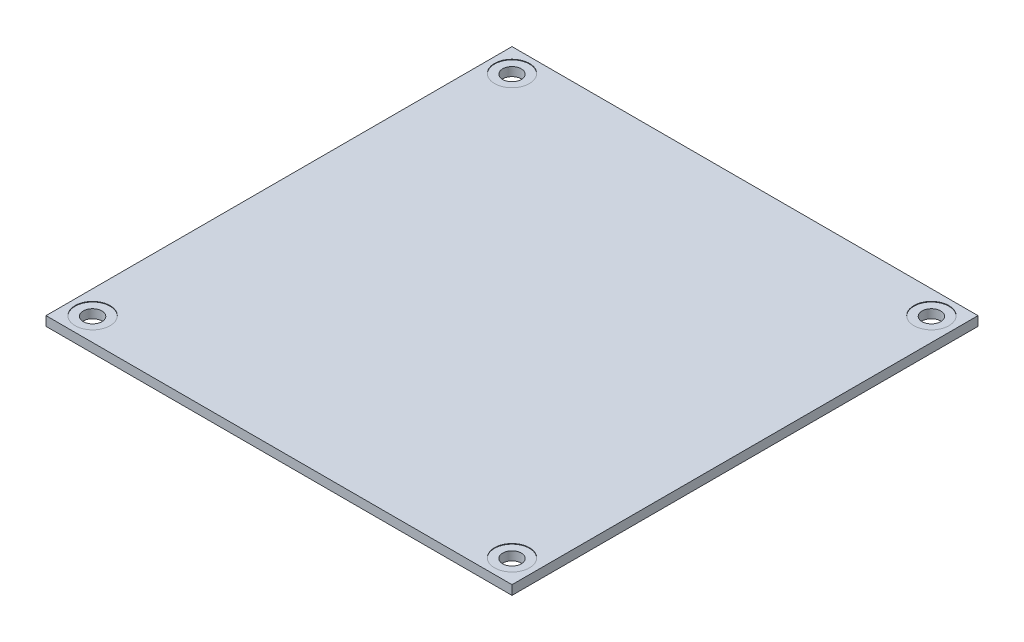
SolidWorks part; units mm, degrees
ref_plane "Front Plane" through (0, 0, 0) normal (0, 0, 1) x (1, 0, 0)
ref_plane "Top Plane" through (0, 0, 0) normal (0, 1, 0) x (1, 0, 0)
ref_plane "Right Plane" through (0, 0, 0) normal (1, 0, 0) x (0, 0, -1)
sketch "Sketch1" plane through (0, 0, 0) normal (0, 1, 0) x (1, 0, 0)
  line L1 (-40, 40) -> (40, 40)
  line L3 (-40, 40) -> (-40, -40)
  line L4 (-40, -40) -> (40, -40)
  line L5 (40, 40) -> (40, -40)
  line L6 (-40, 40) -> (40, -40) construction
  line L7 (-40, -40) -> (40, 40) construction
  point P0 (0, 0)
  dimension "D1" = 80
  dimension "D2" = 80
extrude "Boss-Extrude1" add sketch "Sketch1" along normal blind 1.6 contours L1 L5 L4 L3
sketch "Sketch5" plane through (0, 1.6, 0) normal (0, 1, 0) x (1, 0, 0)
  line L0 (0, 40) -> (0, -40) construction
  line L1 (-40, 40) -> (40, 40) construction
  line L2 (-40, -40) -> (40, -40) construction
  line L3 (-40, 0) -> (40, 0) construction
  line L4 (-40, 40) -> (-40, -40) construction
  line L5 (40, 40) -> (40, -40) construction
  line L6 (-36, 40) -> (-36, 36) construction
  line L7 (-40, 36) -> (-36, 36) construction
  line L8 (40, 36) -> (36, 36) construction
  line L9 (36, 40) -> (36, 36) construction
  line L10 (36, -40) -> (36, -36) construction
  line L11 (40, -36) -> (36, -36) construction
  line L12 (-40, -36) -> (-36, -36) construction
  line L13 (-36, -40) -> (-36, -36) construction
  circle A0 centre (-36, 36) radius 3
  circle A1 centre (36, 36) radius 3
  circle A2 centre (36, -36) radius 3
  circle A3 centre (-36, -36) radius 3
  point P25 (0, 0)
  dimension "D1" = 4
  dimension "D2" = 4
extrude "Cut-Extrude1" cut sketch "Sketch5" against normal blind 0.1
sketch "Sketch6" plane through (0, 1.6, 0) normal (0, 1, 0) x (1, 0, 0)
  line L0 (0, 40) -> (0, -40) construction
  line L1 (-40, 40) -> (40, 40) construction
  line L2 (-40, -40) -> (40, -40) construction
  line L3 (40, 0) -> (-40, 0) construction
  line L4 (-40, 40) -> (-40, -40) construction
  line L5 (40, 40) -> (40, -40) construction
  circle A0 centre (-36, 36) radius 1.6
  circle A1 centre (36, 36) radius 1.6
  circle A2 centre (36, -36) radius 1.6
  circle A3 centre (-36, -36) radius 1.6
  point P24 (0, 0)
  dimension "D1" = 4
extrude "Cut-Extrude2" cut sketch "Sketch6" against normal blind 1.6
